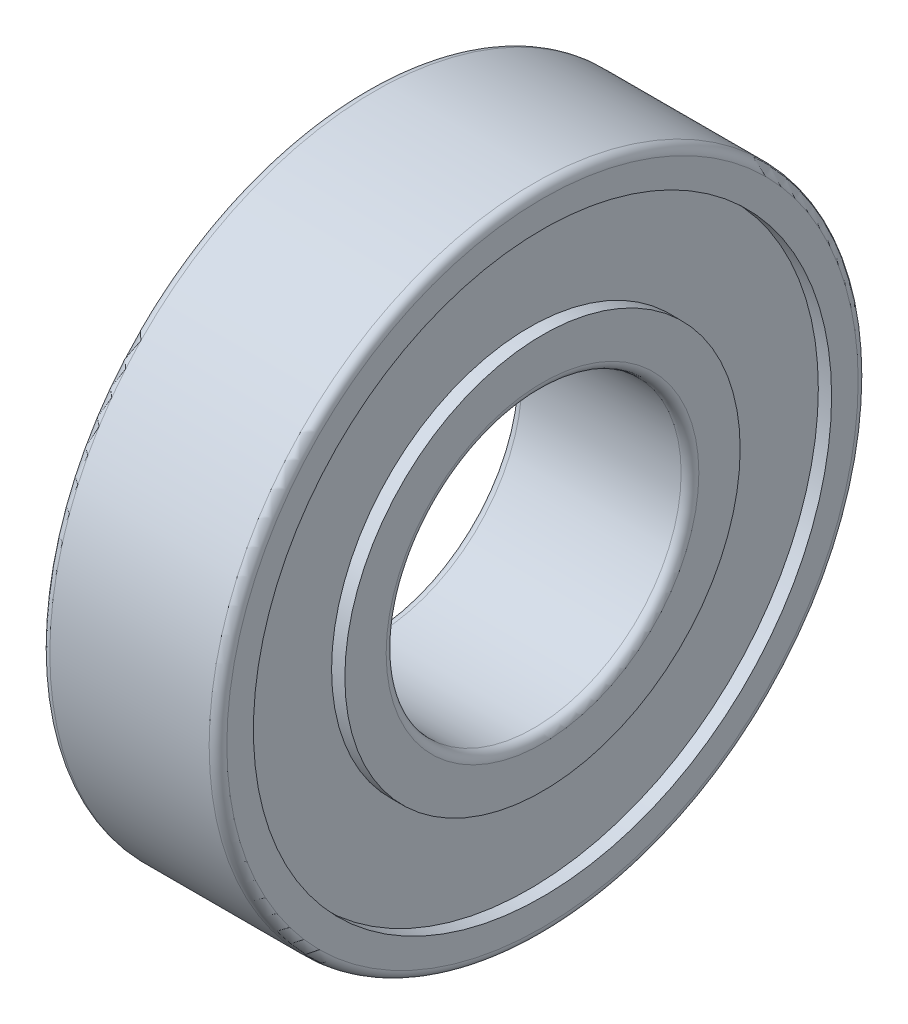
SolidWorks part; units mm, degrees
ref_plane "Front Plane" through (0, 0, 0) normal (0, 0, 1) x (1, 0, 0)
ref_plane "Top Plane" through (0, 0, 0) normal (0, 1, 0) x (1, 0, 0)
ref_plane "Right Plane" through (0, 0, 0) normal (1, 0, 0) x (0, 0, -1)
sketch "Sketch1" plane through (0, 0, 0) normal (0, 0, 1) x (1, 0, 0)
  line L0 (0.3, 5) -> (5.7, 5)
  line L1 (6, 5.3) -> (6, 6.7)
  line L2 (6, 6.7) -> (5.55, 6.7)
  line L3 (5.55, 6.7) -> (5.55, 9.8)
  line L4 (5.55, 9.8) -> (6, 9.8)
  line L5 (6, 9.8) -> (6, 10.7)
  line L6 (5.7, 11) -> (0.3, 11)
  line L7 (0, 10.7) -> (0, 9.8)
  line L8 (0, 9.8) -> (0.45, 9.8)
  line L9 (0.45, 9.8) -> (0.45, 6.7)
  line L10 (0.45, 6.7) -> (0, 6.7)
  line L11 (0, 6.7) -> (0, 5.3)
  line L12 (-0.0013, 0) -> (6.0013, 0) construction
  arc A0 (0, 5.3) -> (0.3, 5) centre (0.3, 5.3) ccw
  arc A1 (5.7, 5) -> (6, 5.3) centre (5.7, 5.3) ccw
  arc A2 (6, 10.7) -> (5.7, 11) centre (5.7, 10.7) ccw
  arc A3 (0.3, 11) -> (0, 10.7) centre (0.3, 10.7) ccw
revolve "Revolve1" add sketch "Sketch1" angle 360 about L12
